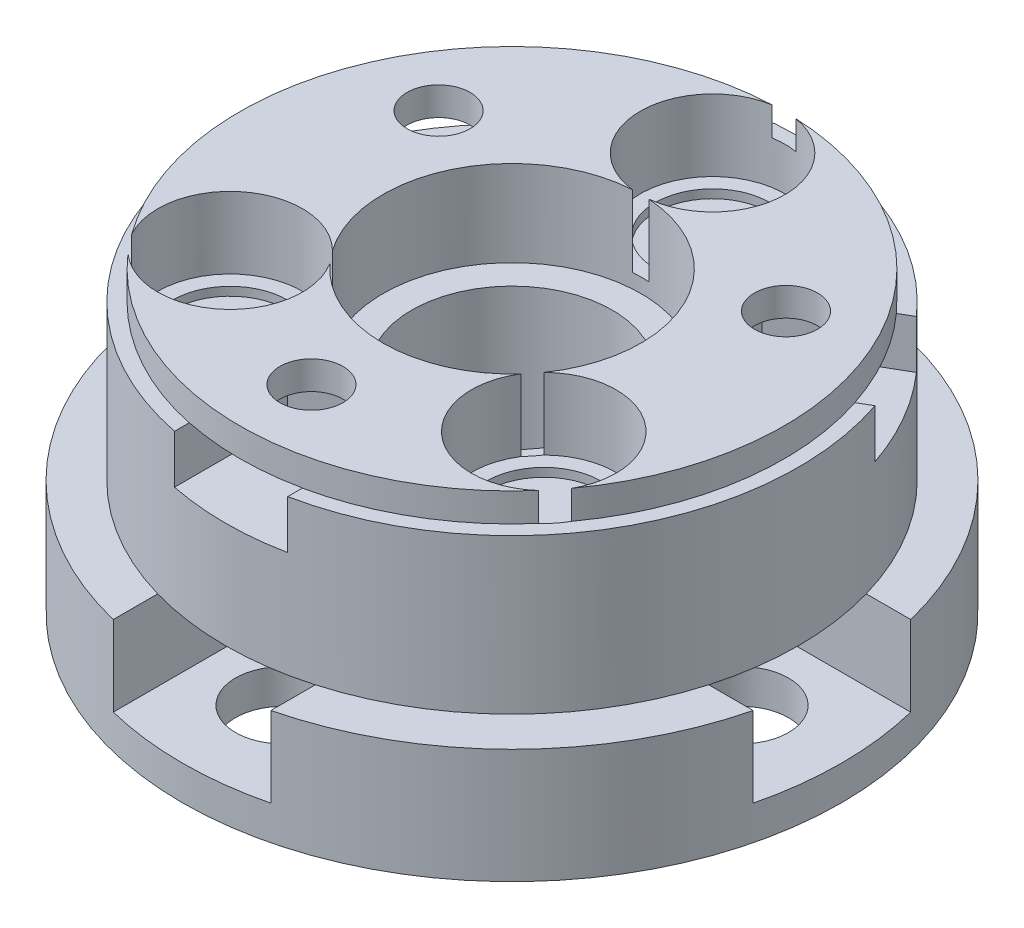
SolidWorks part; units mm, degrees
ref_plane "Front Plane" through (0, 0, 0) normal (0, 0, 1) x (1, 0, 0)
ref_plane "Top Plane" through (0, 0, 0) normal (0, 1, 0) x (1, 0, 0)
ref_plane "Right Plane" through (0, 0, 0) normal (1, 0, 0) x (0, 0, -1)
sketch "Sketch2" plane through (0, 0, 0) normal (0, 1, 0) x (1, 0, 0)
  circle A0 centre (0, 0) radius 11.5
  dimension "D1" = 23
extrude "Boss-Extrude1" add sketch "Sketch2" along normal blind 1
sketch "Sketch3" plane through (0, 1, 0) normal (0, 1, 0) x (1, 0, 0)
  circle A0 centre (0, 0) radius 10
  dimension "D1" = 20
extrude "Boss-Extrude2" add sketch "Sketch3" along normal blind 4
ref_plane "Plane1" through (0, 4.8958, 0) normal (0, -1, 0) x (-1, 0, 0)
sketch "Sketch4" plane through (0, 4.8958, 0) normal (0, -1, 0) x (-1, 0, 0)
  circle A0 centre (0, 0) radius 7 construction
  circle A1 centre (0, 7) radius 2.525
  dimension "D1" = 14
  dimension "D2" = 5.05
extrude "Cut-Extrude1" cut sketch "Sketch4" against normal through all
sketch "Sketch5" plane through (0, 4.8958, 0) normal (0, 1, 0) x (1, 0, 0)
  circle A0 centre (0, 7) radius 2
  dimension "D1" = 4
extrude "Cut-Extrude2" cut sketch "Sketch5" against normal blind 0.3
ref_axis "Axis1" through (0, 5, 0) along (0, -1, 0)
pattern_circular "CirPattern1" count 14 over 360 about axis through (0, 5, 0) along (0, -1, 0) skipping 1, 2, 3, 4, 6, 7, 8, 10, 11, 12, 13 of "Cut-Extrude1", "Cut-Extrude2"
sketch "Sketch7" plane through (0, 4.8958, 0) normal (0, 1, 0) x (1, 0, 0)
  circle A0 centre (5.4728, -4.3644) radius 2.525 construction
  circle A1 centre (0, 0) radius 10
  circle A3 centre (-5.4728, -4.3644) radius 2.525 construction
  circle A4 centre (0, 7) radius 2.525 construction
  circle A5 centre (5.4728, -4.3644) radius 2.525
  circle A6 centre (-5.4728, -4.3644) radius 2.525
  circle A7 centre (0, 7) radius 2.525
  circle A9 centre (0, 0) radius 10
  dimension "D1" = 0
extrude "Boss-Extrude4" add sketch "Sketch7" along normal blind 1.5
sketch "Sketch6" plane through (0, 6.3958, 0) normal (0, 1, 0) x (1, 0, 0)
  circle A0 centre (0, 0) radius 4.5 construction
  arc A1 (-0.4128, 9.491) -> (-0.284, 4.491) centre (0, 7) ccw
  circle A2 centre (0, 0) radius 9.5 construction
  arc A3 (-3.6883, -2.578) -> (-7.6778, -5.5948) centre (-5.4728, -4.3644) ccw
  arc A4 (3.3341, -3.0222) -> (7.163, -6.2403) centre (5.4728, -4.3644) ccw
  arc A5 (0.284, 4.491) -> (0.4128, 9.491) centre (0, 7) ccw
  arc A6 (-7.163, -6.2403) -> (-3.3341, -3.0222) centre (-5.4728, -4.3644) ccw
  arc A7 (7.6778, -5.5948) -> (3.6883, -2.578) centre (5.4728, -4.3644) ccw
  arc A8 (-3.6883, -2.578) -> (-0.284, 4.491) centre (0, 0) cw
  arc A9 (-7.6778, -5.5948) -> (-0.4128, 9.491) centre (0, 0) cw
  arc A12 (-3.3341, -3.0222) -> (3.3341, -3.0222) centre (0, 0) ccw
  arc A13 (-7.163, -6.2403) -> (7.163, -6.2403) centre (0, 0) ccw
  arc A14 (0.284, 4.491) -> (3.6883, -2.578) centre (0, 0) cw
  arc A15 (0.4128, 9.491) -> (7.6778, -5.5948) centre (0, 0) cw
  dimension "D1" = 9
  dimension "D2" = 5.05
  dimension "D3" = 19
extrude "Boss-Extrude3" add sketch "Sketch6" along normal up to surface (0.998 mm away)
sketch "Sketch8" plane through (0, 7.3938, 0) normal (0, 1, 0) x (1, 0, 0)
  circle A0 centre (0, -7) radius 1.1 construction
  circle A1 centre (0, -7) radius 1.1
extrude "Cut-Extrude3" cut sketch "Sketch8" against normal offset from surface (2.69 mm away) 12.2
sketch "Sketch9" plane through (0, 4.7038, 0) normal (0, 1, 0) x (1, 0, 0)
  line L0 (-1.975, -8.1403) -> (-1.975, -11.3291)
  line L1 (0, -9.2805) -> (1.975, -8.1403) construction
  line L2 (1.975, -8.1403) -> (1.975, -5.8597)
  line L3 (1.975, -5.8597) -> (0, -4.7195)
  line L4 (0, -4.7195) -> (-1.975, -5.8597)
  line L5 (-1.975, -5.8597) -> (-1.975, -8.1403)
  line L6 (-1.975, -8.1403) -> (0, -9.2805) construction
  line L7 (-1.975, -11.3291) -> (1.975, -11.3291)
  line L8 (1.975, -11.3291) -> (1.975, -8.1403)
  circle A0 centre (0, -7) radius 1.975 construction
  circle A1 centre (0, 0) radius 11.5 construction
  dimension "D1" = 3.95
extrude "Cut-Extrude4" cut sketch "Sketch9" along normal blind 1.7 contours L7 L8 L2 L3 L4 L5 L0
pattern_circular "CirPattern2" count 3 over 360 about axis through (0, 0, 0) along (0, 1, 0) of "Cut-Extrude4", "Cut-Extrude3"
sketch "Sketch10" plane through (0, 0, 0) normal (0, -1, 0) x (1, 0, 0)
  circle A0 centre (0, 0) radius 8 construction
  circle A1 centre (0, 8) radius 1.35
  dimension "D1" = 16
  dimension "D2" = 2.7
sketch "Sketch11" plane through (0, 0, 0) normal (0, -1, 0) x (1, 0, 0)
  circle A1 centre (0, 0) radius 11.5
  circle A2 centre (0, 0) radius 11.5
  dimension "D1" = 0
extrude "Boss-Extrude5" add sketch "Sketch11" along normal blind 3
sketch "Sketch12" plane through (0, -3, 0) normal (0, -1, 0) x (1, 0, 0)
  circle A0 centre (0, 8) radius 1.65
  dimension "D1" = 3.3
extrude "Cut-Extrude5" cut sketch "Sketch12" against normal up to surface (4 mm away) up to face at (0, 1, 10)
sketch "Sketch13" plane through (0, 1, 0) normal (0, 1, 0) x (1, 0, 0)
  line L0 (-2.75, -9.5877) -> (-2.75, -11.5)
  line L1 (0, -11.1754) -> (2.75, -9.5877) construction
  line L2 (2.75, -9.5877) -> (2.75, -6.4123)
  line L3 (2.75, -6.4123) -> (0, -4.8246)
  line L4 (0, -4.8246) -> (-2.75, -6.4123)
  line L5 (-2.75, -6.4123) -> (-2.75, -9.5877)
  line L6 (-2.75, -9.5877) -> (0, -11.1754) construction
  line L7 (-2.75, -11.5) -> (2.75, -11.5)
  line L8 (2.75, -11.5) -> (2.75, -9.5877)
  circle A0 centre (0, -8) radius 2.75 construction
  circle A1 centre (0, 0) radius 11.5 construction
  dimension "D1" = 5.5
extrude "Cut-Extrude6" cut sketch "Sketch13" against normal blind 2.8
pattern_circular "CirPattern3" count 4 over 360 about axis through (0, 0, 0) along (0, 1, 0) of "Cut-Extrude5", "Cut-Extrude6"
sketch "Sketch14" [suppressed] plane through (0, 0, 0) normal (0, -1, 0) x (1, 0, 0)
  circle A0 centre (0, 0) radius 7 construction
  circle A1 centre (0, 7) radius 1.4
  dimension "14" = 14
  dimension "D2" = 2.8
extrude "Cut-Extrude7" [suppressed] cut sketch "Sketch14" against normal blind 4
sketch "Sketch15" [suppressed] plane through (0, 4, 0) normal (0, -1, 0) x (1, 0, 0)
  line L1 (0, 4.0555) -> (2.55, 5.5278)
  line L2 (2.55, 5.5278) -> (2.55, 8.4722)
  line L3 (2.55, 8.4722) -> (0, 9.9445) construction
  line L4 (0, 9.9445) -> (-2.55, 8.4722) construction
  line L5 (-2.55, 8.4722) -> (-2.55, 5.5278)
  line L6 (-2.55, 5.5278) -> (0, 4.0555)
  line L9 (2.55, 11.5) -> (-2.55, 11.5)
  line L10 (-2.55, 8.4722) -> (-2.55, 11.5)
  line L11 (2.55, 8.4722) -> (2.55, 11.5)
  circle A0 centre (0, 7) radius 2.55 construction
  circle A2 centre (0, 0) radius 11.5 construction
  dimension "D1" = 5.1
extrude "Cut-Extrude8" [suppressed] cut sketch "Sketch15" along normal blind 2.4
pattern_circular "CirPattern4" [suppressed] count 3 over 360 about axis through (0, 5, 0) along (0, -1, 0)
sketch "Sketch16" plane through (0, 6.3958, 0) normal (0, 1, 0) x (1, 0, 0)
  circle A0 centre (0, 0) radius 4.5
  arc A1 (3.6883, -2.578) -> (0.284, 4.491) centre (0, 0) ccw construction
extrude "Cut-Extrude9" cut sketch "Sketch16" against normal blind 2
sketch "Sketch17" plane through (0, 4.3958, 0) normal (0, 1, 0) x (1, 0, 0)
  circle A0 centre (0, 0) radius 3.5
  dimension "D1" = 7
extrude "Cut-Extrude10" cut sketch "Sketch17" against normal through all
